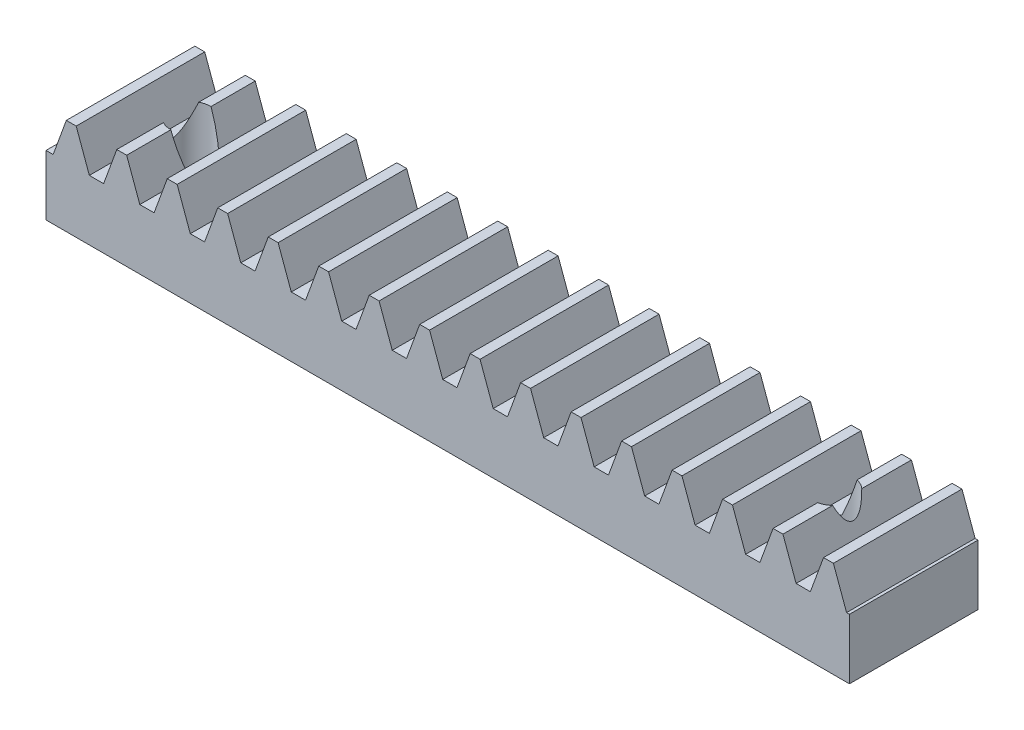
SolidWorks part; units mm, degrees
ref_plane "Plane1" through (0, 0, 0) normal (0, 0, 1) x (1, 0, 0)
ref_plane "Plane2" through (0, 0, 0) normal (0, 1, 0) x (1, 0, 0)
ref_plane "Plane3" through (0, 0, 0) normal (1, 0, 0) x (0, 0, -1)
sketch "HoldingSke" plane through (0, 0, 0) normal (0, 1, 0) x (1, 0, 0)
  line L0 (0, 0) -> (0.1392, 0.9903)
  line L1 (-15, 0) -> (100, 0) construction
  line L2 (0, 0) -> (-2.1039, 2.3779)
  line L3 (0, 0) -> (-11.863, 4.5341)
  line L4 (0, 0) -> (8.2587, 2.5249)
  line L5 (0, 0) -> (-23.7986, -8.8762)
  line L6 (0, 0) -> (-10.5278, -7.1032)
  line L9 (-71.009, 38.7566) -> (-24.0243, 55.8576)
  line L10 (-76.2, 3.3779) -> (-71.2, 3.3779)
  line L11 (0, 0) -> (-7, 0)
  line L12 (-76.2, 101.6) -> (-76.162, 101.6)
  line L13 (24.9733, 27.94) -> (52.9518, 28.4284)
  line L14 (24.9733, 27.94) -> (24.9743, 27.94)
  line L15 (24.9733, 27.94) -> (100.4006, 29.5858)
  circle A0 centre (0, 0) radius 19.05
  circle A1 centre (0, 0) radius 2.5
  circle A2 centre (0, 0) radius 12.7
  dimension "MPH" = 5
  dimension "Diameter" = 38.1
  dimension "Num_teeth" = 17
  dimension "Pitch" = 1
  dimension "Width" = 7
  dimension "Show_teeth" = 998
  dimension "Thickness" = 12.7
  dimension "Ap" = 20
  dimension "Pitch_height" = 5
  dimension "Backlash" = 0.038
  dimension "Addendum_fac" = 1
  dimension "Dedendum_fac" = 1.25
  dimension "Clearance_fac" = 0.25
  dimension "Dedendum_add" = 0.001
  dimension "Length" = 50
  dimension "Module" = 1
sketch "BlankSke" plane through (0, 0, 0) normal (0, 0, 1) x (1, 0, 0)
  line L1 (0, 0) -> (50, 0)
  line L2 (0, 0) -> (0, 6)
  line L3 (0, 6) -> (50, 6)
  line L4 (50, 0) -> (50, 6)
  dimension "Length" = 50
  dimension "Blank_height" = 6
extrude "Blank" add sketch "BlankSke" against normal blind 8
sketch "TooCutSkeIll" plane through (0, 0, 0) normal (0, 0, 1) x (1, 0, 0)
  line L0 (-1.2538, 5.9737) -> (-0.5045, 3.9152)
  line L1 (-0.2687, 3.75) -> (0.2687, 3.75)
  line L2 (0.5045, 3.9152) -> (1.2538, 5.9737)
  line L3 (50, 6) -> (0, 6) construction
  line L4 (0, 0) -> (0, 64.897) construction
  line L5 (-13.208, 5) -> (12.954, 5) construction
  line L6 (0, 0) -> (50, 0) construction
  line L7 (0.8994, 5) -> (0.8994, 48.7463) construction
  line L8 (-0.8994, 5) -> (-0.8994, 48.7463) construction
  line L9 (1.2914, 6) -> (1.2914, 6.0254)
  line L10 (-1.2914, 6) -> (-1.2914, 6.0254)
  line L11 (-1.2914, 6.0254) -> (1.2914, 6.0254)
  arc A0 (0.2687, 3.75) -> (0.5045, 3.9152) centre (0.2687, 4.001) ccw
  arc A1 (-0.5045, 3.9152) -> (-0.2687, 3.75) centre (-0.2687, 4.001) ccw
  arc A2 (1.2914, 6) -> (1.2538, 5.9737) centre (1.2914, 5.96) ccw
  arc A3 (-1.2538, 5.9737) -> (-1.2914, 6) centre (-1.2914, 5.96) ccw
  dimension "Root_fillet" = 0.251
  dimension "Break_rad" = 0.04
  dimension "Pitch_height" = 5
  dimension "Gap_width" = 1.7988
  dimension "Dedendum" = 1.25
  dimension "Addendum_plus" = 1.0254
  dimension "Pressure_angle" = 20
extrude "ToothCutIll" [suppressed] cut sketch "TooCutSkeIll" against normal through all
sketch "TooCutSkeSim" plane through (0, 0, 0) normal (0, 0, 1) x (1, 0, 0)
  line L0 (0.4444, 3.75) -> (-0.4444, 3.75)
  line L1 (1.2726, 6.0254) -> (0.4444, 3.75)
  line L2 (0, 17.4625) -> (0, 53.467) construction
  line L3 (1.2726, 6.0254) -> (-1.2726, 6.0254)
  line L6 (-1.2726, 6.0254) -> (-0.4444, 3.75)
  line L9 (-0.8994, 5) -> (0.8994, 5) construction
  line L10 (0, 0) -> (50, 0) construction
  line L11 (0.8994, 5) -> (0.8994, 53.467) construction
  line L12 (-0.8994, 5) -> (-0.8994, 53.467) construction
  dimension "Pitch_height" = 5
  dimension "Pressure_angle" = 20
  dimension "Gap_width" = 1.7988
  dimension "Dedendum" = 1.25
  dimension "Addendum_plus" = 1.0254
extrude "ToothCutSim" cut sketch "TooCutSkeSim" against normal through all
pattern_linear "TeethCuts" count 17 spacing 3.1416 along (1, 0, 0) of "ToothCutIll", "ToothCutSim"
sketch "Sketch1" plane through (0, 0, 0) normal (0, -1, 0) x (-1, 0, 0)
  line L0 (-50, 8) -> (-50, 0) construction
  line L1 (0, 0) -> (-50, 0) construction
  line L2 (0, 8) -> (0, 0) construction
  circle A0 centre (-45, 4) radius 1.25
  circle A1 centre (-5, 4) radius 1.25
  dimension "D1" = 2.5
  dimension "D2" = 5
  dimension "D3" = 4
  dimension "D4" = 2.5
  dimension "D5" = 5
  dimension "D6" = 4
extrude "Cut-Extrude1" cut sketch "Sketch1" against normal blind 10
equation "' \"Module@HoldingSke\" = 6.35"
equation "' \"Num_teeth@HoldingSke\" = 12"
equation "' \"Ap@HoldingSke\" =  20"
equation "' \"Width@HoldingSke\" = 0.25 * 25.4"
equation "' \"Show_teeth@HoldingSke\" = 500"
equation "' \"Backlash@HoldingSke\" = 0.009 * 25.4"
equation "' \"Addendum_fac@HoldingSke\" = 1.0"
equation "' \"Dedendum_fac@HoldingSke\" = 1.25"
equation "' \"Dedendum_add@HoldingSke\" = 0.00005 * 25.4"
equation "' \"Clearance_fac@HoldingSke\" = 0.25"
equation "' \"Pitch_height@HoldingSke\" = 1 * 25.4"
equation "' \"Length@HoldingSke\" = 4.71 * 25.4"
equation "\"Pitch@HoldingSke\" = 1 / \"Module@HoldingSke\""
equation "\"MPH@HoldingSke\" = \"Dedendum_fac@HoldingSke\" / \"Pitch@HoldingSke\" + 2 * \"Dedendum_add@HoldingSke\" + 0.002 * 25.4"
equation "\"MPH@HoldingSke\" = ((sgn( \"MPH@HoldingSke\" - \"Pitch_height@HoldingSke\")+1)*( \"MPH@HoldingSke\" - \"Pitch_height@HoldingSke\"))/2 + \"Pitch_height@HoldingSke\""
equation "\"Blank_height@BlankSke\"=6"
equation "\"Length@BlankSke\" =  \"Length@HoldingSke\""
equation "\"Face_width@Blank\"=8"
equation "\"Pressure_angle@TooCutSkeIll\" = \"Ap@HoldingSke\""
equation "\"Addendum_plus@TooCutSkeIll\" =  \"Addendum_fac@HoldingSke\"  / \"Pitch@HoldingSke\" + 0.001 *25.4"
equation "\"Dedendum@TooCutSkeIll\" = \"Dedendum_fac@HoldingSke\"  / \"Pitch@HoldingSke\""
equation "\"Pitch_height@TooCutSkeIll\" =  \"MPH@HoldingSke\""
equation "\"Gap_width@TooCutSkeIll\" = 3.14159265 / 2 / \"Pitch@HoldingSke\" + 6 * \"Backlash@HoldingSke\""
equation "\"Pressure_angle@TooCutSkeSim\" = \"Ap@HoldingSke\""
equation "\"Addendum_plus@TooCutSkeSim\" =  \"Addendum_fac@HoldingSke\"  / \"Pitch@HoldingSke\" + 0.001 * 25.4"
equation "\"Dedendum@TooCutSkeSim\" = \"Dedendum_fac@HoldingSke\"  / \"Pitch@HoldingSke\""
equation "\"Pitch_height@TooCutSkeSim\" =  \"MPH@HoldingSke\""
equation "\"Gap_width@TooCutSkeSim\" = 3.14159265 / 2 / \"Pitch@HoldingSke\" + 6 * \"Backlash@HoldingSke\""
equation "\"Root_fillet@TooCutSkeIll\" = \"Clearance_fac@HoldingSke\" / \"Pitch@HoldingSke\" + \"Dedendum_add@HoldingSke\""
equation "\"Break_rad@TooCutSkeIll\" = 0.02 / \"Pitch@HoldingSke\" * 2"
equation "\"Linear_pitch@TeethCuts\" = 3.14159265 / \"Pitch@HoldingSke\""
equation "\"Num_teeth@HoldingSke\" = int( ( \"Length@HoldingSke\" + 0 ) / (3.14159265 / \"Pitch@HoldingSke\")) + 0.9999  + 1"
equation " \"Num_teeth@TeethCuts\" = int( \"Show_teeth@HoldingSke\" ) + 1"
equation " \"Num_teeth@TeethCuts\" = ((sgn( \"Num_teeth@TeethCuts\" - \"Num_teeth@HoldingSke\" )-1)*( \"Num_teeth@TeethCuts\" - \"Num_teeth@HoldingSke\" ))/-2+ \"Num_teeth@HoldingSke\""
equation " \"Num_teeth@TeethCuts\" = ((sgn( \"Num_teeth@TeethCuts\" - 2.0)+1)*( \"Num_teeth@TeethCuts\" - 2.0))/2 +2.0"
